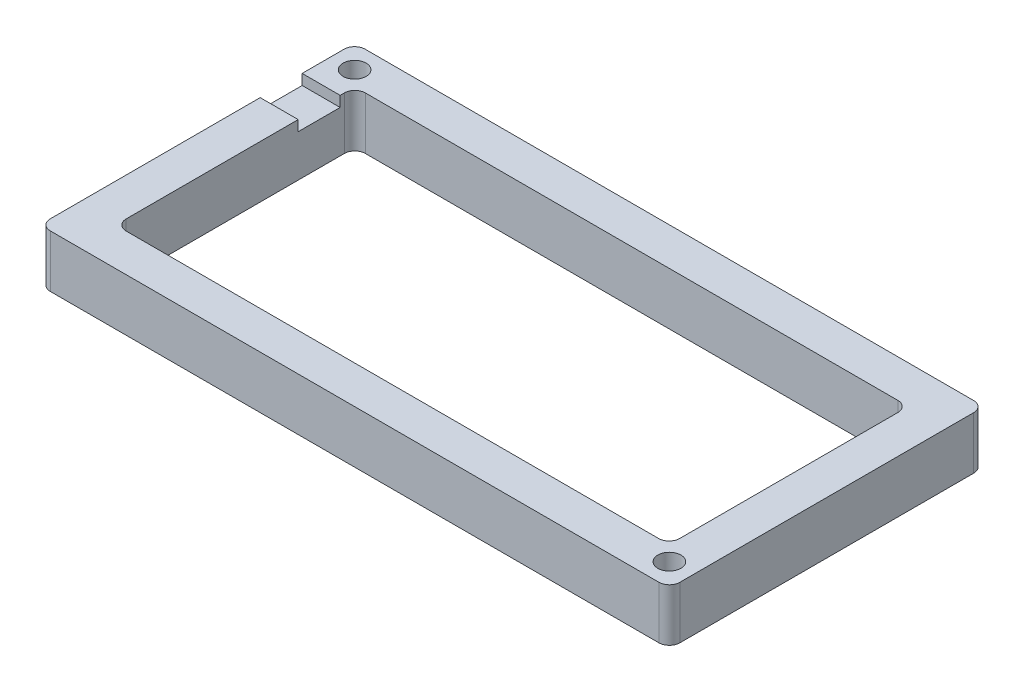
SolidWorks part; units mm, degrees
ref_plane "Front Plane" through (0, 0, 0) normal (0, 0, 1) x (1, 0, 0)
ref_plane "Top Plane" through (0, 0, 0) normal (0, 1, 0) x (1, 0, 0)
ref_plane "Right Plane" through (0, 0, 0) normal (1, 0, 0) x (0, 0, -1)
sketch "Sketch1" plane through (0, 0, 0) normal (0, 1, 0) x (1, 0, 0)
  line L1 (-76.2, 38.1) -> (76.2, 38.1)
  line L2 (-76.2, 38.1) -> (-76.2, -38.1)
  line L3 (-76.2, -38.1) -> (76.2, -38.1)
  line L4 (76.2, 38.1) -> (76.2, -38.1)
  line L5 (-76.2, 38.1) -> (76.2, -38.1) construction
  line L6 (-76.2, -38.1) -> (76.2, 38.1) construction
  point P0 (0, 0)
  point P6 (0, 0)
  point P7 (0, 0)
  dimension "D1" = 152.4
  dimension "D2" = 76.2
extrude "Boss-Extrude1" add sketch "Sketch1" along normal blind 12.7
fillet "Fillet1" radius 2.54 4 edges at (76.2, 6.35, 38.1) (76.2, 6.35, -38.1) (-76.2, 6.35, -38.1) (-76.2, 6.35, 38.1)
sketch "Sketch2" plane through (-76.2, 0, 0) normal (-1, 0, 0) x (0, 0, 1)
  line L0 (-35.56, 12.7) -> (35.56, 12.7) construction
  line L1 (-25.4, 12.7) -> (-15.24, 12.7)
  line L2 (-25.4, 12.7) -> (-25.4, 10.16)
  line L3 (-25.4, 10.16) -> (-15.24, 10.16)
  line L4 (-15.24, 12.7) -> (-15.24, 10.16)
  line L6 (41.91, 0) -> (-41.91, 0) construction
  dimension "D1" = 2.54
  dimension "D2" = 10.16
  dimension "D3" = 15.24
sketch "Sketch3" plane through (0, 0, 0) normal (0, 1, 0) x (1, 0, 0)
  line L0 (76.2, -35.56) -> (76.2, 35.56) construction
  line L1 (-66.9975, 28.956) -> (66.9975, 28.956)
  line L2 (-66.9975, 28.956) -> (-66.9975, -28.956)
  line L3 (-66.9975, -28.956) -> (66.9975, -28.956)
  line L4 (66.9975, 28.956) -> (66.9975, -28.956)
  line L5 (-66.9975, 28.956) -> (66.9975, -28.956) construction
  line L6 (-66.9975, -28.956) -> (66.9975, 28.956) construction
  line L7 (73.66, 38.1) -> (-73.66, 38.1) construction
  point P1 (0, 0)
  dimension "D1" = 9.2025
  dimension "D2" = 9.144
extrude "Cut-Extrude4" cut sketch "Sketch3" along normal through all
fillet "Fillet2" radius 2.54 4 edges at (-66.9975, 6.35, 28.956) (-66.9975, 6.35, -28.956) (66.9975, 6.35, -28.956) (66.9975, 6.35, 28.956)
extrude "Cut-Extrude5" cut sketch "Sketch2" against normal blind 12.7
sketch "Sketch4" plane through (0, 0, 0) normal (0, 1, 0) x (1, 0, 0)
  line L0 (-76.2, 35.56) -> (-76.2, 25.4) construction
  line L1 (73.66, 38.1) -> (-73.66, 38.1) construction
  circle A0 centre (-70.612, 32.512) radius 2.794
  dimension "D3" = 5.588
  dimension "D1" = 5.588
  dimension "D2" = 5.588
extrude "Cut-Extrude6" cut sketch "Sketch4" along normal blind 12.7
sketch "Sketch5" plane through (0, 0, 0) normal (0, 1, 0) x (1, 0, 0)
  line L0 (-73.66, -38.1) -> (73.66, -38.1) construction
  line L1 (76.2, -35.56) -> (76.2, 35.56) construction
  circle A0 centre (70.612, -32.512) radius 2.794
  dimension "D3" = 5.588
  dimension "D1" = 5.588
  dimension "D2" = 5.588
extrude "Cut-Extrude7" cut sketch "Sketch5" along normal blind 12.7
